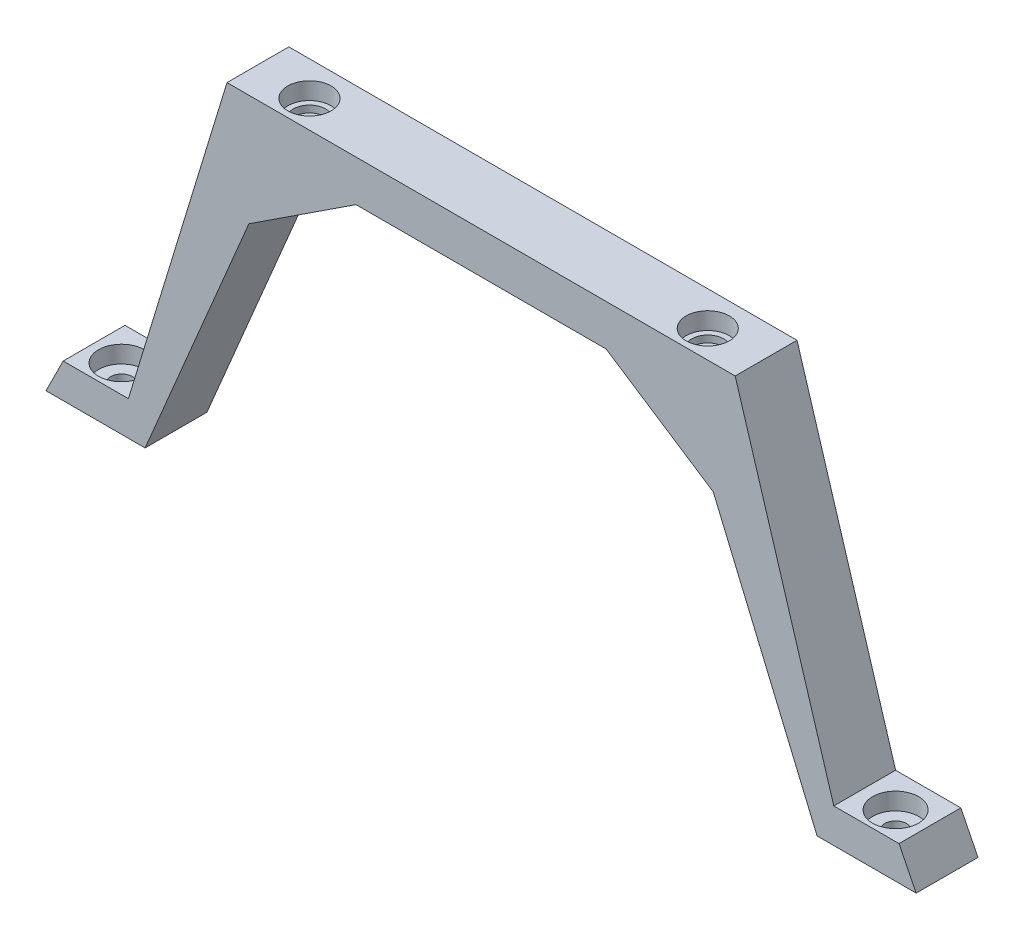
SolidWorks part; units mm, degrees
ref_plane "前视基准面" through (0, 0, 0) normal (0, 0, 1) x (1, 0, 0)
ref_plane "上视基准面" through (0, 0, 0) normal (0, 1, 0) x (1, 0, 0)
ref_plane "右视基准面" through (0, 0, 0) normal (1, 0, 0) x (0, 0, -1)
sketch "草图1" plane through (0, 0, 0) normal (0, 0, 1) x (1, 0, 0)
  line L0 (33.8113, 38.6957) -> (33.8113, 7.0528) construction
  line L1 (-3.1887, 13.0528) -> (33.8113, 13.0528)
  line L2 (-3.1887, 13.0528) -> (-17.5487, -33.9913)
  line L3 (15.602, 7.0528) -> (0, -3.1586)
  line L4 (33.8113, 13.0528) -> (33.8113, 7.0528)
  line L6 (-15.1144, -38.9913) -> (0, -3.1586)
  line L7 (33.8113, 7.0528) -> (15.602, 7.0528)
  line L10 (-17.5487, -33.9913) -> (-27.0458, -33.9913)
  line L12 (-27.0458, -33.9913) -> (-29.5458, -38.9913)
  line L13 (-29.5458, -38.9913) -> (-15.1144, -38.9913)
  point P0 (33.8113, 10.0528)
extrude "凸台-拉伸1" add sketch "草图1" along normal blind 10
ref_plane "基准面3" through (33.8113, 0, 0) normal (1, 0, 0) x (0, 0, -1)
mirror "镜向1" about plane through (33.8113, 13.0528, 10) normal (-1, 0, 0) of "凸台-拉伸1"
ref_plane "基准面1" through (0, 0, 5) normal (0, 0, 1) x (1, 0, 0)
sketch "草图5" plane through (0, 0, 5) normal (0, 0, 1) x (1, 0, 0)
  line L0 (33.8113, 20.2752) -> (33.8113, -16.9928) construction
  line L1 (70.8113, 13.0528) -> (-3.1887, 13.0528) construction
  line L2 (7.9613, 13.0528) -> (7.9613, 10.5528)
  line L3 (7.9613, 10.5528) -> (7.1613, 10.5528)
  line L4 (7.1613, 10.5528) -> (7.1613, 9.5528)
  line L5 (7.1613, 9.5528) -> (6.3613, 9.5528)
  line L6 (4.8113, 13.0528) -> (4.8113, 2.5746) construction
  line L7 (4.8113, 13.0528) -> (7.9613, 13.0528)
  line L8 (6.3613, 9.5528) -> (4.8113, 9.5528)
  line L9 (4.8113, 9.5528) -> (4.8113, 13.0528)
  point P2 (4.8113, 13.0528)
  point P3 (62.8113, 13.0274)
  point P6 (7.9613, 13.0528)
  point P13 (6.3613, 9.5528)
  dimension "D2" = 29
  dimension "D3" = 3.15
revolve "切除-旋转7" cut sketch "草图5" angle 360 about L9
sketch "草图7" plane through (0, 9.5528, 0) normal (0, 1, 0) x (1, 0, 0)
  circle A0 centre (4.8113, -5) radius 1.55
  dimension "D1" = 3.1
extrude "切除-拉伸1" cut sketch "草图7" against normal through all
ref_plane "基准面2" through (0, -5.9472, 0) normal (0, 1, 0) x (1, 0, 0)
sketch "草图8" plane through (0, -5.9472, 0) normal (0, 1, 0) x (1, 0, 0)
  line L1 (8.3331, -5) -> (6.5722, -1.95)
  line L2 (6.5722, -1.95) -> (3.0504, -1.95)
  line L3 (3.0504, -1.95) -> (1.2895, -5)
  line L4 (1.2895, -5) -> (3.0504, -8.05)
  line L5 (3.0504, -8.05) -> (6.5722, -8.05)
  line L6 (6.5722, -8.05) -> (8.3331, -5)
  circle A0 centre (4.8113, -5) radius 3.05 construction
  dimension "D1" = 6.1
extrude "切除-拉伸2" cut sketch "草图8" along normal blind 8.5
sketch "草图19" plane through (0, 13.0528, 0) normal (0, 1, 0) x (1, 0, 0)
  line L4 (97.1684, -10) -> (97.1684, -9.004)
  line L5 (97.1684, -9.004) -> (-29.5458, -9.004)
  line L6 (-29.5458, -9.004) -> (-29.5458, -10)
  line L17 (-29.5458, -10) -> (97.1684, -10)
extrude "切除-拉伸14" cut sketch "草图19" against normal through all
sketch "草图22" plane through (0, -33.9913, 0) normal (0, 1, 0) x (1, 0, 0)
  line L0 (-17.5487, -9.004) -> (-17.5487, 0) construction
  line L1 (-27.0458, -9.004) -> (-17.5487, -9.004) construction
  circle A0 centre (-22.5487, -5.004) radius 1.575
  dimension "D1" = 5
  dimension "D2" = 4
  dimension "D3" = 3.15
extrude "切除-拉伸15" cut sketch "草图22" against normal blind 10
sketch "草图23" plane through (0, -33.9913, 0) normal (0, 1, 0) x (1, 0, 0)
  circle A0 centre (-22.5487, -5.004) radius 3.35
  dimension "D1" = 6.7
extrude "切除-拉伸16" cut sketch "草图23" against normal blind 2.5
mirror "镜向2" about plane through (33.8113, 0, 0) normal (1, 0, 0) of "切除-拉伸1", "切除-拉伸2", "切除-旋转7", "切除-拉伸15", "切除-拉伸16"
